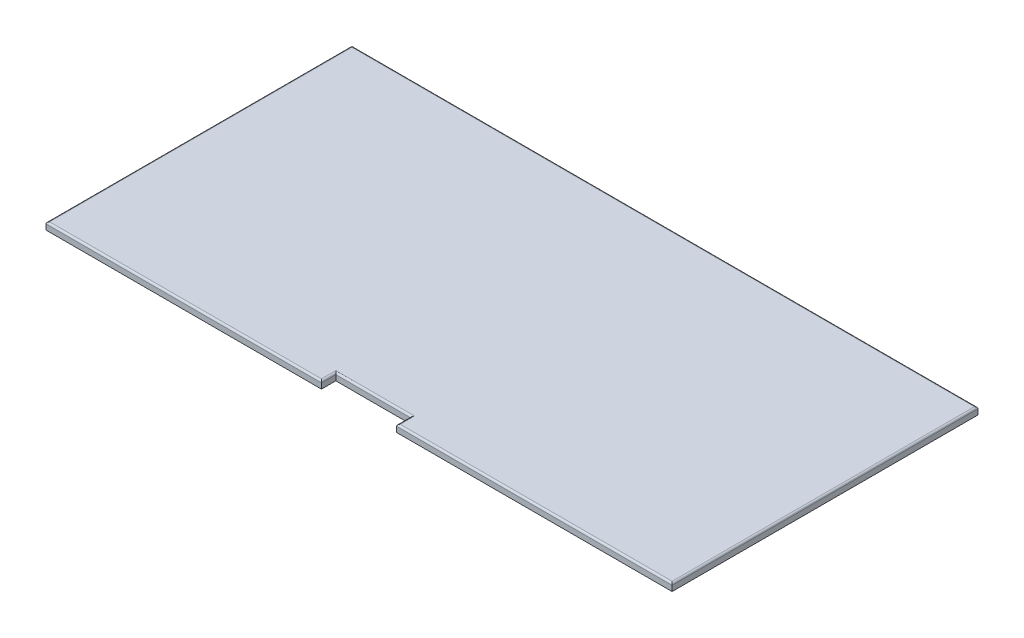
SolidWorks part; units mm, degrees
material "1060 Alloy"
ref_plane "Front Plane" through (0, 0, 0) normal (0, 0, 1) x (1, 0, 0)
ref_plane "Top Plane" through (0, 0, 0) normal (0, 1, 0) x (1, 0, 0)
ref_plane "Right Plane" through (0, 0, 0) normal (1, 0, 0) x (0, 0, -1)
sketch "Sketch1" plane through (0, 0, 0) normal (0, 1, 0) x (1, 0, 0)
  line L1 (-875, 427.5) -> (875, 427.5)
  line L2 (-875, 427.5) -> (-875, -427.5)
  line L3 (-875, -427.5) -> (875, -427.5)
  line L4 (875, 427.5) -> (875, -427.5)
  line L5 (-875, 427.5) -> (875, -427.5) construction
  line L6 (-875, -427.5) -> (875, 427.5) construction
  point P0 (0, 0)
  dimension "D1" = 855
  dimension "D2" = 1750
extrude "Boss-Extrude1" add sketch "Sketch1" along normal blind 20
sketch "Sketch2" plane through (0, 20, 0) normal (0, 1, 0) x (1, 0, 0)
  line L0 (-875, -427.5) -> (875, -427.5) construction
  line L1 (-105, -387.5) -> (105, -387.5)
  line L2 (-105, -387.5) -> (-105, -467.5)
  line L3 (-105, -467.5) -> (105, -467.5)
  line L4 (105, -387.5) -> (105, -467.5)
  line L5 (-105, -387.5) -> (105, -467.5) construction
  line L6 (-105, -467.5) -> (105, -387.5) construction
  point P0 (0, -427.5)
  dimension "D1" = 210
  dimension "D2" = 80
extrude "Cut-Extrude1" cut sketch "Sketch2" against normal blind 20
fillet "Fillet1" radius 5 8 edges at (105, 20, 407.5) (0, 20, 387.5) (-105, 20, 407.5) (875, 20, 0) (0, 20, -427.5) (-875, 20, 0) (490, 20, 427.5) (-490, 20, 427.5)
